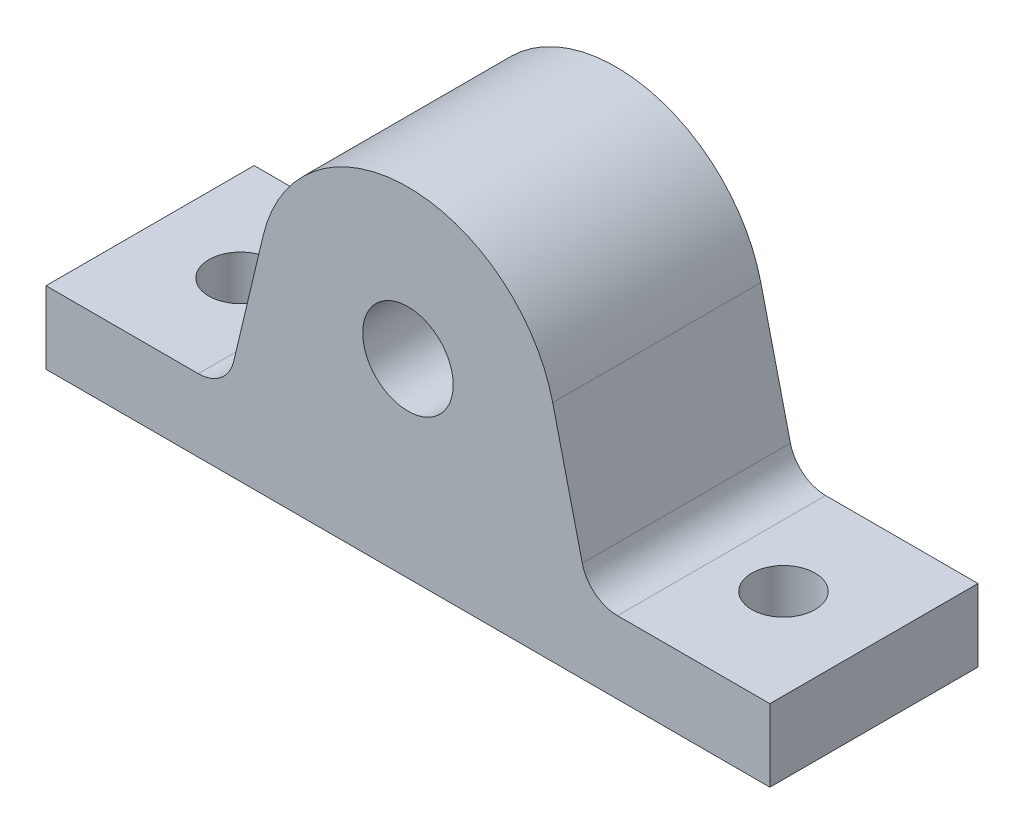
SolidWorks part; units mm, degrees
ref_plane "Front" through (0, 0, 0) normal (0, 0, 1) x (1, 0, 0)
ref_plane "Top" through (0, 0, 0) normal (0, 1, 0) x (1, 0, 0)
ref_plane "Right" through (0, 0, 0) normal (1, 0, 0) x (0, 0, -1)
sketch "Sketch1" plane through (0, 0, 0) normal (0, 0, 1) x (1, 0, 0)
  line L0 (-63.5, 0) -> (63.5, 0)
  line L1 (63.5, 0) -> (63.5, 12.7)
  line L2 (63.5, 12.7) -> (31.75, 12.7)
  line L3 (31.75, 12.7) -> (25.4, 39.3823)
  line L4 (-63.5, 0) -> (-63.5, 12.7)
  line L5 (-63.5, 12.7) -> (-31.75, 12.7)
  line L6 (-31.75, 12.7) -> (-25.4, 39.3823)
  line L7 (0, 33.3375) -> (0, 0) construction
  arc A0 (-25.4, 39.3823) -> (25.4, 39.3823) centre (0, 33.3375) cw
  dimension "D1" = 50.8
  dimension "D2" = 33.3375
  dimension "D3" = 12.7
  dimension "D4" = 63.5
  dimension "D5" = 127
extrude "Extrude1" add sketch "Sketch1" along normal mid plane 36.5125
fillet "Fillet1" radius 6.35 2 edges at (-31.75, 12.7, 0) (31.75, 12.7, 0)
sketch "Sketch3" plane through (0, 0, 18.2562) normal (0, 0, 1) x (1, 0, 0)
  line L0 (-63.5, 0) -> (63.5, 0) construction
  circle A0 centre (0, 33.3375) radius 7.9375
  arc A2 (25.4, 39.3823) -> (-25.4, 39.3823) centre (0, 33.3375) ccw construction
  dimension "D1" = 15.875
extrude "Cut-Extrude1" cut sketch "Sketch3" against normal through all
sketch "Sketch4" plane through (0, 12.7, 0) normal (0, 1, 0) x (-1, 0, 0)
  line L0 (0, -18.2562) -> (0, 18.2563) construction
  line L3 (63.5, -18.2562) -> (-63.5, -18.2562) construction
  line L4 (63.5, 18.2562) -> (-63.5, 18.2562) construction
  circle A0 centre (-47.625, 0) radius 5.5562
  circle A1 centre (47.625, 0) radius 5.5562
  dimension "D1" = 11.1125
  dimension "D2" = 95.25
extrude "Cut-Extrude2" cut sketch "Sketch4" against normal through all
